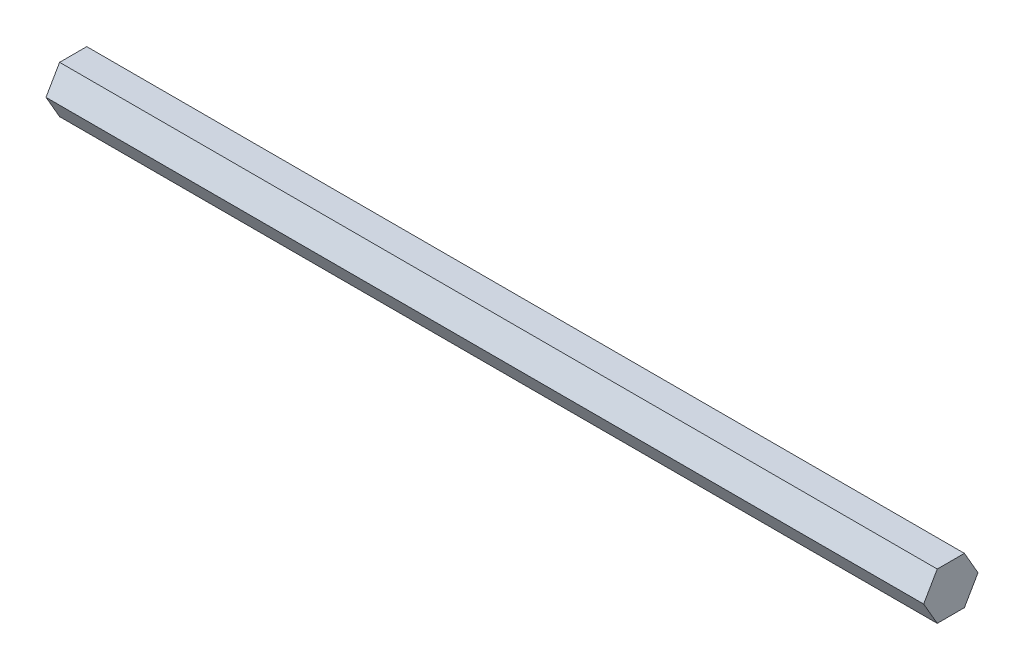
SolidWorks part; units mm, degrees
ref_plane "Front Plane" through (0, 0, 0) normal (0, 0, 1) x (1, 0, 0)
ref_plane "Top Plane" through (0, 0, 0) normal (0, 1, 0) x (1, 0, 0)
ref_plane "Right Plane" through (0, 0, 0) normal (1, 0, 0) x (0, 0, -1)
sketch "Sketch1" plane through (0, 0, 0) normal (1, 0, 0) x (0, 0, -1)
  line L1 (7.3323, 0) -> (3.6662, 6.35)
  line L2 (3.6662, 6.35) -> (-3.6662, 6.35)
  line L3 (-3.6662, 6.35) -> (-7.3323, 0)
  line L4 (-7.3323, 0) -> (-3.6662, -6.35)
  line L5 (-3.6662, -6.35) -> (3.6662, -6.35)
  line L6 (3.6662, -6.35) -> (7.3323, 0)
  circle A0 centre (0, 0) radius 6.35 construction
  dimension "D1" = 12.7
extrude "Boss-Extrude1" add sketch "Sketch1" along normal blind 236.85
